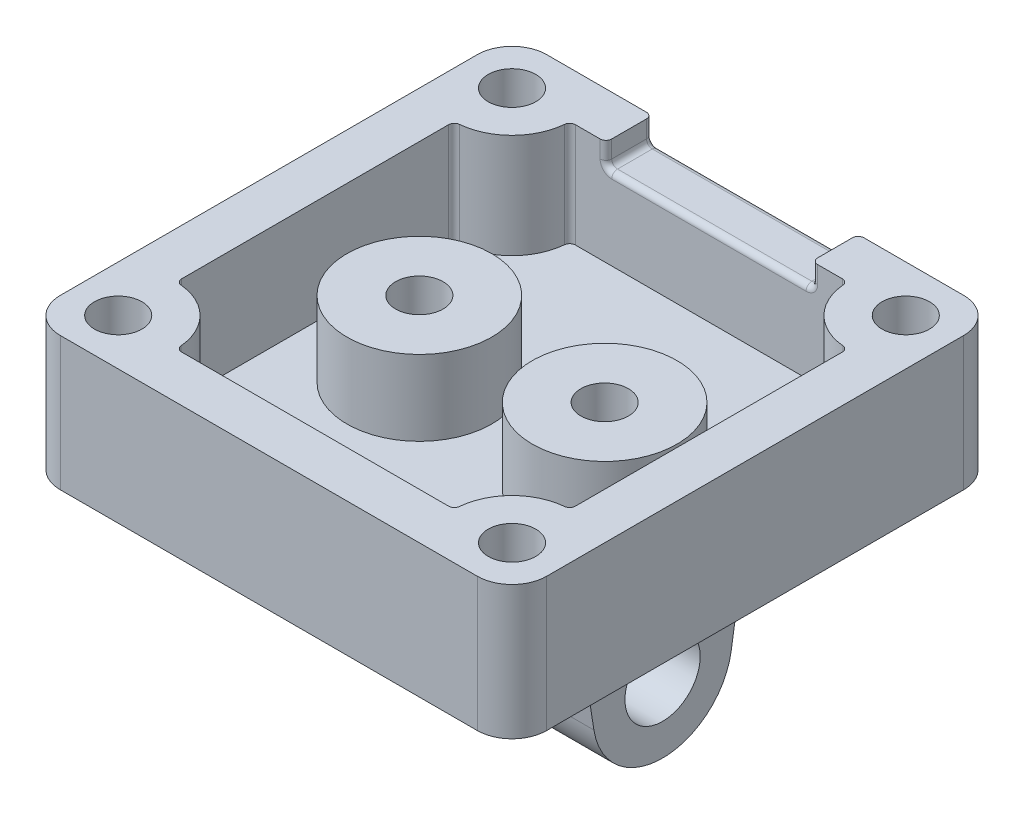
SolidWorks part; units mm, degrees
material "ABS"
ref_plane "Front Plane" through (0, 0, 0) normal (0, 0, 1) x (1, 0, 0)
ref_plane "Top Plane" through (0, 0, 0) normal (0, 1, 0) x (1, 0, 0)
ref_plane "Right Plane" through (0, 0, 0) normal (1, 0, 0) x (0, 0, -1)
sketch "Sketch1" plane through (0, 0, 0) normal (0, 1, 0) x (1, 0, 0)
  line L1 (-21, 21) -> (21, 21)
  line L2 (-21, 21) -> (-21, -21)
  line L3 (-21, -21) -> (21, -21)
  line L4 (21, 21) -> (21, -21)
  line L5 (-21, 21) -> (21, -21) construction
  line L6 (-21, -21) -> (21, 21) construction
  point P0 (0, 0)
  dimension "D1" = 42
  dimension "D2" = 42
extrude "Boss-Extrude1" add sketch "Sketch1" along normal blind 2.54
sketch "Sketch2" plane through (0, 2.54, 0) normal (0, 1, 0) x (1, 0, 0)
  line L26 (-21, 21) -> (21, 21)
  line L44 (-21, 21) -> (-21, -21)
  line L45 (-21, -21) -> (21, -21)
  line L49 (21, 21) -> (21, -21)
  line L50 (-21, 21) -> (21, -21) construction
  line L51 (-21, -21) -> (21, 21) construction
  line L55 (-17, 11.5228) -> (-17, -11.5228)
  line L56 (-11.5228, -17) -> (11.5228, -17)
  line L57 (17, 11.5228) -> (17, -11.5228)
  line L58 (-11.5228, 17) -> (11.5228, 17)
  line L63 (-17, 17) -> (-17, -17) construction
  line L64 (-17, -17) -> (17, -17) construction
  line L65 (17, 17) -> (17, -17) construction
  line L66 (-17, 17) -> (17, 17) construction
  line L68 (-13.4645, 13.4645) -> (13.4645, 13.4645) construction
  line L69 (-13.4645, 13.4645) -> (-13.4645, -13.4645) construction
  line L70 (-13.4645, -13.4645) -> (13.4645, -13.4645) construction
  line L71 (13.4645, 13.4645) -> (13.4645, -13.4645) construction
  line L72 (-13.4645, 13.4645) -> (13.4645, -13.4645) construction
  line L73 (-13.4645, -13.4645) -> (13.4645, 13.4645) construction
  arc A0 (-16.5455, -12.0207) -> (-12.0207, -16.5455) centre (-17, -17) cw
  arc A2 (12.0207, -16.5455) -> (16.5455, -12.0207) centre (17, -17) cw
  arc A4 (16.5455, 12.0207) -> (12.0207, 16.5455) centre (17, 17) cw
  arc A6 (-12.0207, 16.5455) -> (-16.5455, 12.0207) centre (-17, 17) cw
  arc A8 (-16.5455, -12.0207) -> (-17, -11.5228) centre (-16.5, -11.5228) cw
  arc A9 (-12.0207, -16.5455) -> (-11.5228, -17) centre (-11.5228, -16.5) ccw
  arc A10 (12.0207, -16.5455) -> (11.5228, -17) centre (11.5228, -16.5) cw
  arc A11 (16.5455, -12.0207) -> (17, -11.5228) centre (16.5, -11.5228) ccw
  arc A12 (16.5455, 12.0207) -> (17, 11.5228) centre (16.5, 11.5228) cw
  arc A13 (12.0207, 16.5455) -> (11.5228, 17) centre (11.5228, 16.5) ccw
  arc A14 (-12.0207, 16.5455) -> (-11.5228, 17) centre (-11.5228, 16.5) cw
  arc A15 (-16.5455, 12.0207) -> (-17, 11.5228) centre (-16.5, 11.5228) ccw
  point P0 (0, 0)
  point P44 (0, 0)
  dimension "D2" = 5
  dimension "D3" = 0.5
  dimension "D1" = 4
  dimension "D4" = 26.9289
  dimension "D5" = 26.9289
extrude "Boss-Extrude2" add sketch "Sketch2" along normal blind 9
ref_plane "Plane1" through (0, 0, 0) normal (1, 0, 0) x (0, 0, -1)
sketch "Sketch4" plane through (-21, 0, 0) normal (-1, 0, 0) x (0, 0, 1)
  line L0 (7.5, 0) -> (5.9271, -10)
  line L1 (-21, 0) -> (21, 0) construction
  line L2 (-5.9271, -10) -> (-7.5, 0)
  line L3 (7.5, 0) -> (-7.5, 0)
  arc A0 (5.9271, -10) -> (-5.9271, -10) centre (0, -9.0677) cw
  circle A1 centre (0, -9.0677) radius 3.25
  point P11 (0, 0)
  point P12 (0, 0)
  dimension "D1" = 6.5
  dimension "D4" = 6
  dimension "D2" = 10
  dimension "D3" = 15
extrude "Boss-Extrude4" [suppressed] add sketch "Sketch4" against normal up to surface (42 mm away)
mirror "Mirror1" [suppressed] about plane through (0, 0, 0) normal (1, 0, 0)
sketch "Sketch13" plane through (0, 0, 0) normal (1, 0, 0) x (0, 0, -1)
  line L3 (-7.5, 0) -> (-5.9271, -10)
  line L4 (5.9271, -10) -> (7.5, 0)
  line L5 (7.5, 0) -> (-7.5, 0)
  line L6 (-7.5, 0) -> (-5.9271, -10)
  line L7 (5.9271, -10) -> (7.5, 0)
  line L8 (7.5, 0) -> (-7.5, 0)
  circle A1 centre (0, -9.0677) radius 3.25
  circle A2 centre (0, -9.0677) radius 3.25
  arc A3 (-5.9271, -10) -> (5.9271, -10) centre (0, -9.0677) ccw
  arc A4 (-5.9271, -10) -> (5.9271, -10) centre (0, -9.0677) ccw
  dimension "D1" = 0
  dimension "D2" = 0
extrude "Boss-Extrude6" add sketch "Sketch13" along normal mid plane 26
sketch "Sketch9" plane through (0, 2.54, 0) normal (0, 1, 0) x (1, 0, 0)
  line L0 (0, -55) -> (0, 55) construction
  line L1 (0, 0) -> (-8, 0) construction
  circle A0 centre (8, 0) radius 2.05
  circle A1 centre (8, 0) radius 6.25
  circle A2 centre (-8, 0) radius 6.25
  circle A3 centre (-8, 0) radius 2.05
  dimension "D1" = 4.1
  dimension "D2" = 4.2
  dimension "D3" = 8
extrude "Boss-Extrude5" add sketch "Sketch9" along normal blind 6.5
sketch "Sketch10" plane through (0, 11.54, 0) normal (0, 1, 0) x (1, 0, 0)
  circle A0 centre (-17, 17) radius 2.05
  circle A1 centre (17, 17) radius 2.05
  circle A2 centre (-17, -17) radius 2.05
  circle A3 centre (17, -17) radius 2.05
  dimension "D1" = 4.1
extrude "Cut-Extrude1" cut sketch "Sketch10" against normal blind 8
sketch "Sketch12" plane through (0, 0, -21) normal (0, 0, -1) x (-1, 0, 0)
  line L0 (-21, 11.54) -> (21, 11.54) construction
  line L1 (8.89, 9.54) -> (-8.89, 9.54)
  line L2 (8.89, 9.54) -> (8.89, 11.54)
  line L3 (8.89, 11.54) -> (-8.89, 11.54)
  line L4 (-8.89, 9.54) -> (-8.89, 11.54)
  line L5 (8.89, 9.54) -> (-8.89, 11.54) construction
  line L6 (8.89, 11.54) -> (-8.89, 9.54) construction
  point P0 (0, 10.54)
  point P7 (0, 11.54)
  point P8 (0, 11.54)
  dimension "D1" = 2
  dimension "D2" = 17.78
extrude "Cut-Extrude2" cut sketch "Sketch12" against normal up to surface (4 mm away) up to face at (0, 7.04, -17)
fillet "Fillet1" radius 3 4 edges at (21, 5.77, 21) (-21, 5.77, 21) (-21, 5.77, -21) (21, 5.77, -21)
fillet "Fillet2" radius 0.5 8 edges at (-8.89, 10.54, -21) (8.89, 10.54, -21) (0, 9.54, -21) (0, 9.54, -17) (-8.89, 10.54, -17) (8.89, 10.54, -17) (8.89, 9.54, -19) (-8.89, 9.54, -19)
fillet "Fillet3" radius 3 2 edges at (0, 0, -7.5) (0, 0, 7.5)
